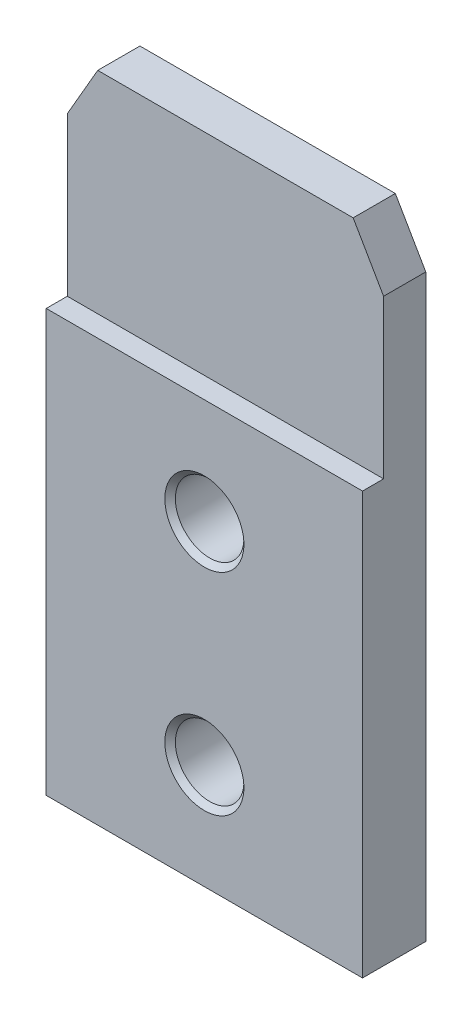
SolidWorks part; units mm, degrees
ref_plane "Спереди" through (0, 0, 0) normal (0, 0, 1) x (1, 0, 0)
ref_plane "Сверху" through (0, 0, 0) normal (0, 1, 0) x (1, 0, 0)
ref_plane "Справа" through (0, 0, 0) normal (1, 0, 0) x (0, 0, -1)
sketch "Эскиз1" plane through (0, 0, 0) normal (0, 0, 1) x (1, 0, 0)
  line L1 (-15, -30) -> (15, -30)
  line L2 (-15, -30) -> (-15, 30)
  line L3 (-15, 30) -> (15, 30)
  line L4 (15, -30) -> (15, 30)
  line L5 (-15, -30) -> (15, 30) construction
  line L6 (-15, 30) -> (15, -30) construction
  circle A0 centre (0, -20) radius 3.25
  circle A1 centre (0, 0) radius 3.25
  point P0 (0, 0)
extrude "Бобышка-Вытянуть1" add sketch "Эскиз1" along normal blind 6
sketch "Эскиз2" plane through (15, 0, 0) normal (-1, 0, 0) x (0, 0, 1)
  line L0 (6, 30) -> (6, 10)
  line L2 (6, 10) -> (4, 10)
  line L4 (6, 30) -> (4, 30)
  line L5 (4, 30) -> (4, 10)
  line L7 (6, 30) -> (0, 30) construction
  line L8 (6, -30) -> (6, 30) construction
extrude "Вырез-Вытянуть1" cut sketch "Эскиз2" along normal through all
chamfer "Фаска1" [suppressed] distance 5 angle 30
chamfer "Фаска2" distance 5 angle 30 1 edges at (-15, 30, 2)
chamfer "Фаска3" distance 5 angle 30 1 edges at (15, 30, 2)
chamfer "Фаска4" distance 0.5 angle 45 4 edges at (3.25, -20, 0) (3.25, -20, 6) (3.25, 0, 0) (3.25, 0, 6)
